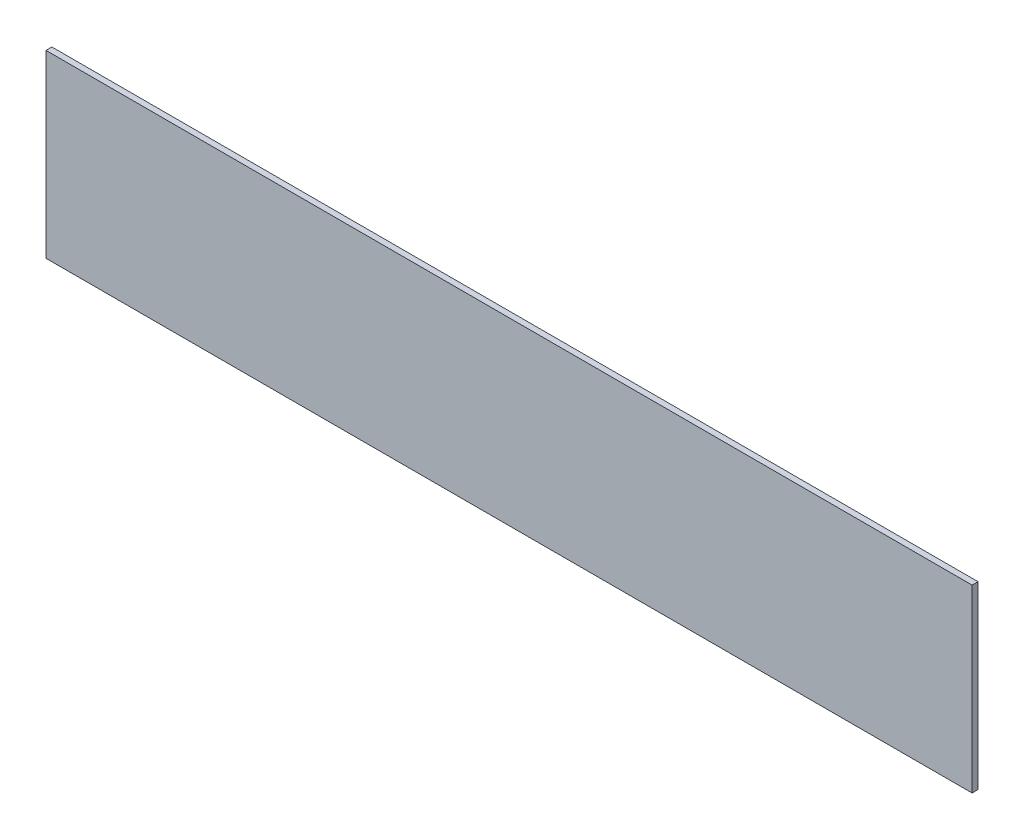
SolidWorks part; units mm, degrees
material "Pine"
ref_plane "Front Plane" through (0, 0, 0) normal (0, 0, 1) x (1, 0, 0)
ref_plane "Top Plane" through (0, 0, 0) normal (0, 1, 0) x (1, 0, 0)
ref_plane "Right Plane" through (0, 0, 0) normal (1, 0, 0) x (0, 0, -1)
sketch "Sketch1" plane through (0, 0, 0) normal (0, 0, 1) x (1, 0, 0)
  line L0 (228.6, -483.0939) -> (-228.6, -483.0939) construction
  line L1 (-228.6, -571.9939) -> (228.6, -571.9939)
  line L2 (-228.6, -571.9939) -> (-228.6, -483.0939)
  line L3 (-228.6, -483.0939) -> (228.6, -483.0939)
  line L4 (228.6, -571.9939) -> (228.6, -483.0939)
  line L5 (228.6, -567.2314) -> (228.6, -487.8564) construction
  line L6 (-228.6, -571.9939) -> (228.6, -571.9939) construction
  line L7 (-228.6, -487.8564) -> (-228.6, -567.2314) construction
extrude "Boss-Extrude1" add sketch "Sketch1" along normal up to surface (2.921 mm away)
